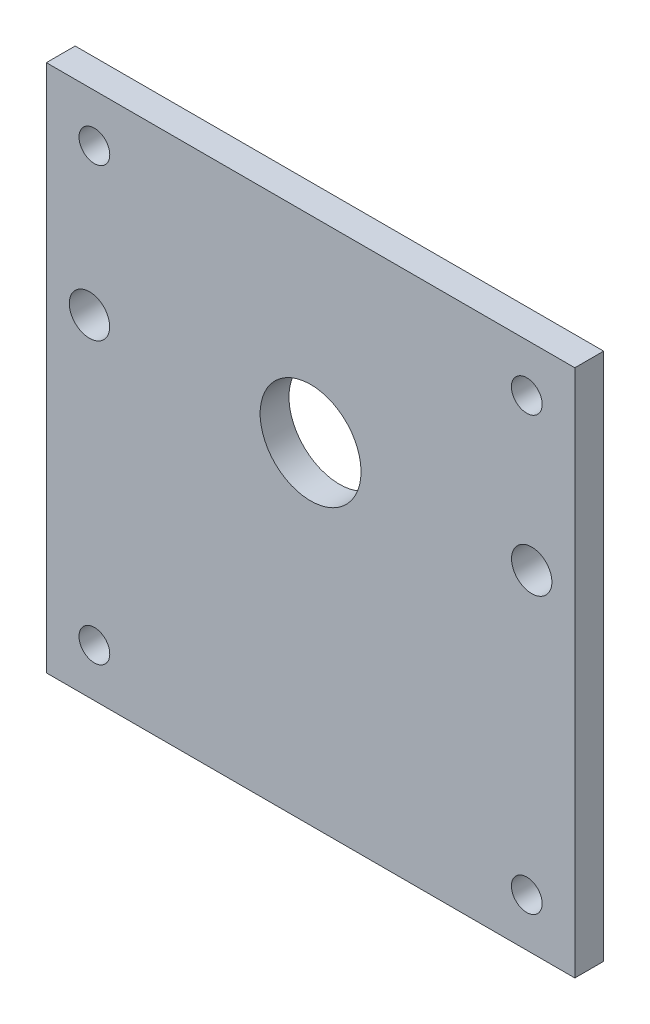
SolidWorks part; units mm, degrees
material "5052-H34"
ref_plane "正面" through (0, 0, 0) normal (0, 0, 1) x (1, 0, 0)
ref_plane "平面" through (0, 0, 0) normal (0, 1, 0) x (1, 0, 0)
ref_plane "右側面" through (0, 0, 0) normal (1, 0, 0) x (0, 0, -1)
sketch "ｽｹｯﾁ1" plane through (0, 0, 0) normal (0, 0, 1) x (1, 0, 0)
  line L0 (0, 0) -> (0, 15.5) construction
  line L1 (-27.5, 22.5) -> (27.5, 22.5) construction
  line L2 (-27.5, 27.5) -> (27.5, 27.5)
  line L3 (-27.5, 27.5) -> (-27.5, -27.5)
  line L4 (-27.5, -27.5) -> (27.5, -27.5)
  line L5 (27.5, 27.5) -> (27.5, -27.5)
  line L6 (-27.5, 27.5) -> (27.5, -27.5) construction
  line L7 (-27.5, -27.5) -> (27.5, 27.5) construction
  line L8 (-27.5, -22.5) -> (27.5, -22.5) construction
  circle A0 centre (0, 0) radius 15.5 construction
  circle A1 centre (0, 7) radius 5.25
  circle A5 centre (-22.5, 22.5) radius 1.6
  circle A6 centre (22.5, 22.5) radius 1.6
  circle A7 centre (-22.5, -22.5) radius 1.6
  circle A8 centre (22.5, -22.5) radius 1.6
  circle A9 centre (-23.0125, 7) radius 2.1
  circle A10 centre (23.0125, 7) radius 2.1
  point P15 (0, 0)
  dimension "D1" = 31
  dimension "D2" = 10.5
  dimension "D10" = 3.2
  dimension "D11" = 3.2
  dimension "D12" = 3.2
  dimension "D13" = 3.2
  dimension "D4" = 4.2
  dimension "D19" = 4.2
  dimension "D3" = 7
  dimension "D6" = 55
  dimension "D7" = 55
  dimension "D8" = 5
  dimension "D9" = 5
  dimension "D14" = 5
  dimension "D15" = 5
  dimension "D16" = 5
  dimension "D17" = 5
  dimension "D5" = 23.0125
  dimension "D18" = 23.0125
extrude "ﾎﾞｽ - 押し出し1" add sketch "ｽｹｯﾁ1" along normal blind 3
equation "\"D18@ｽｹｯﾁ1\"=\"D5@ｽｹｯﾁ1\""
equation "\"D5@ｽｹｯﾁ1\"=46.025/2"
